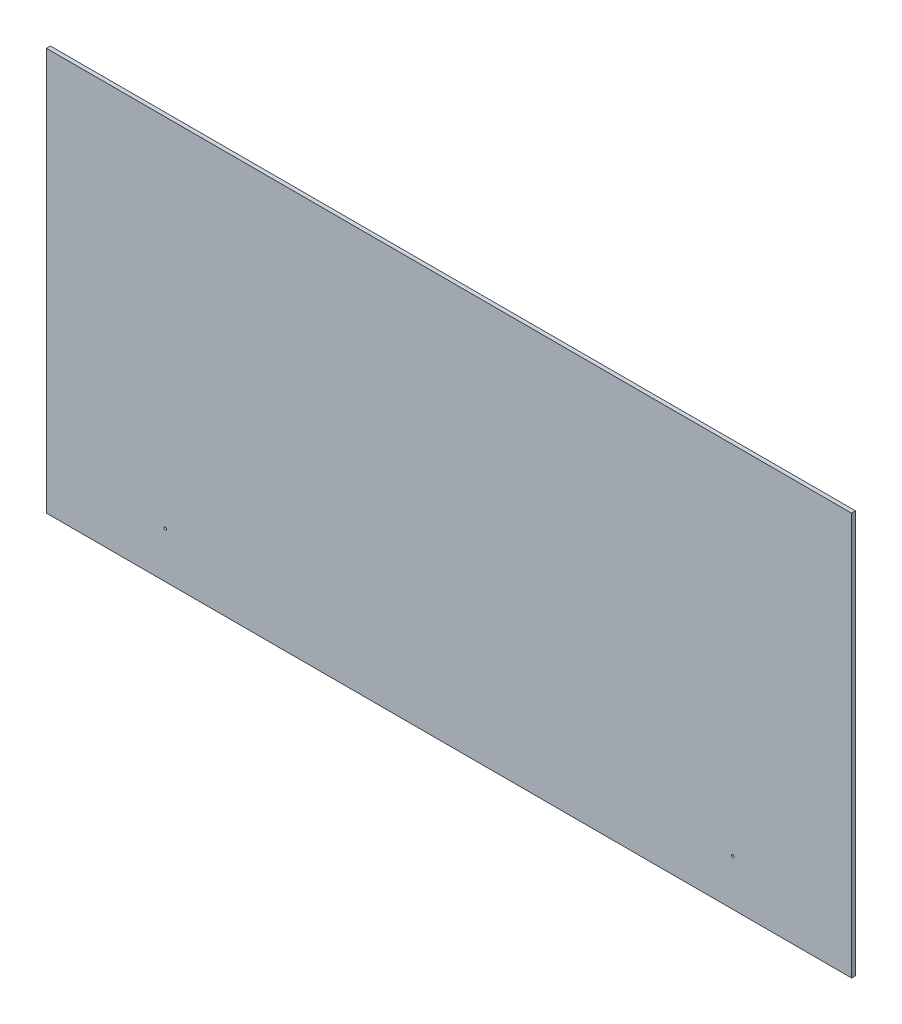
SolidWorks part; units mm, degrees
material "Pin"
ref_plane "Plan de face" through (0, 0, 0) normal (0, 0, 1) x (1, 0, 0)
ref_plane "Plan de dessus" through (0, 0, 0) normal (0, 1, 0) x (1, 0, 0)
ref_plane "Plan de droite" through (0, 0, 0) normal (1, 0, 0) x (0, 0, -1)
sketch "Esquisse1" plane through (0, 0, 0) normal (0, 0, 1) x (1, 0, 0)
  line L1 (0, 0) -> (-1220, 0)
  line L2 (0, 0) -> (0, 610)
  line L3 (0, 610) -> (-1220, 610)
  line L4 (-1220, 0) -> (-1220, 610)
  dimension "D1" = 610
  dimension "D2" = 1220
extrude "Boss.-Extru.1" add sketch "Esquisse1" along normal blind 6
sketch "Esquisse2" plane through (0, 0, 6) normal (0, 0, 1) x (1, 0, 0)
  line L0 (-1220, 610) -> (-1220, 0) construction
  line L1 (-1220, 0) -> (0, 0) construction
  line L2 (-610, 610) -> (-610, 0) construction
  line L3 (0, 610) -> (-1220, 610) construction
  circle A0 centre (-1040, 70) radius 2
  circle A1 centre (-180, 70) radius 2
  dimension "D1" = 4
  dimension "D2" = 180
  dimension "D3" = 70
extrude "Enlèv. mat.-Extru.1" cut sketch "Esquisse2" against normal up to surface (6 mm away) up to face at (-610, 305, 0)
